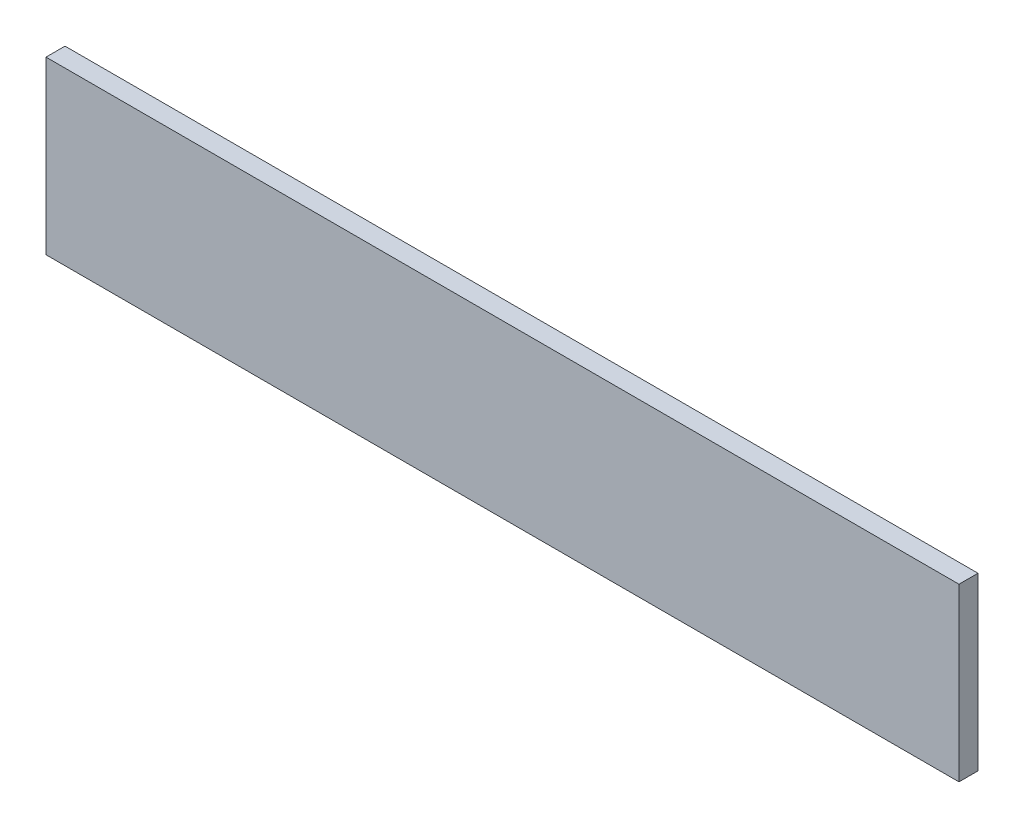
SolidWorks part; units mm, degrees
ref_plane "Front Plane" through (0, 0, 0) normal (0, 0, 1) x (1, 0, 0)
ref_plane "Top Plane" through (0, 0, 0) normal (0, 1, 0) x (1, 0, 0)
ref_plane "Right Plane" through (0, 0, 0) normal (1, 0, 0) x (0, 0, -1)
sketch "Sketch1" plane through (0, 0, 0) normal (0, 0, 1) x (1, 0, 0)
  line L1 (-304.8, -57.15) -> (304.8, -57.15)
  line L2 (-304.8, -57.15) -> (-304.8, 57.15)
  line L3 (-304.8, 57.15) -> (304.8, 57.15)
  line L4 (304.8, -57.15) -> (304.8, 57.15)
  line L5 (-304.8, -57.15) -> (304.8, 57.15) construction
  line L6 (-304.8, 57.15) -> (304.8, -57.15) construction
  point P0 (0, 0)
  dimension "D1" = 114.3
  dimension "D2" = 609.6
extrude "Boss-Extrude1" add sketch "Sketch1" along normal blind 12.7
